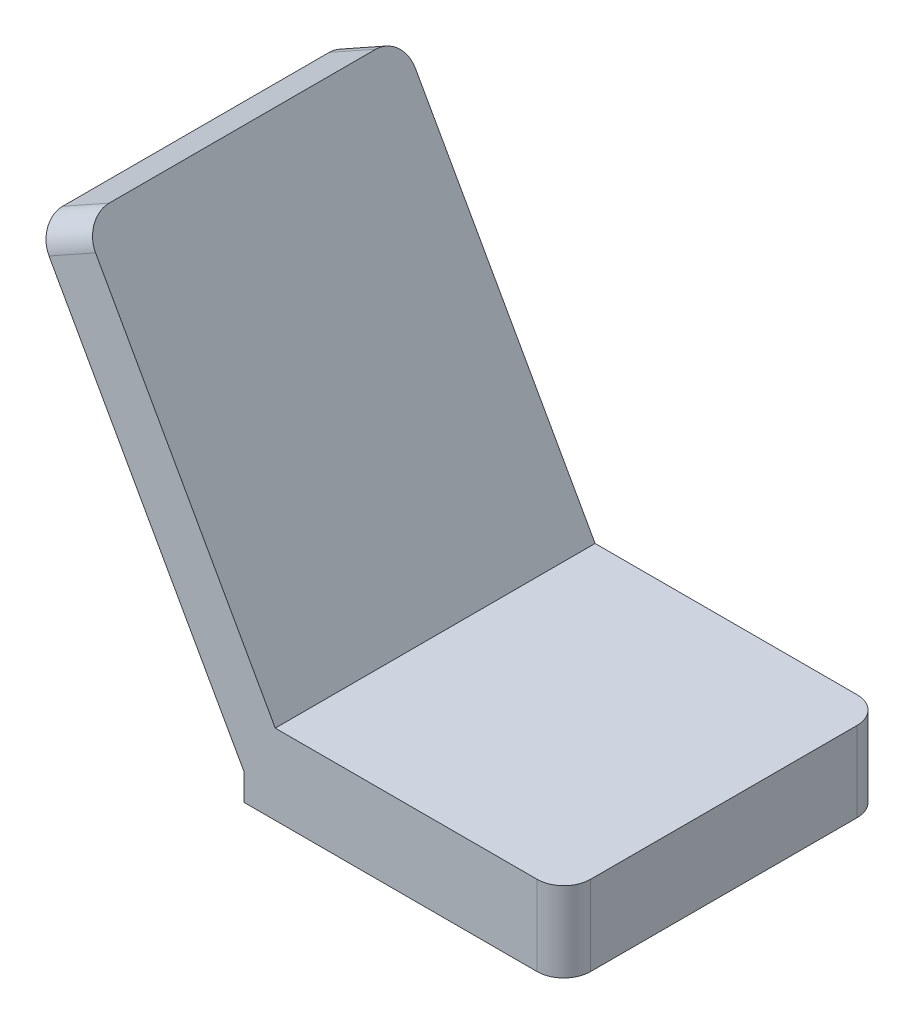
SolidWorks part; units mm, degrees
ref_plane "Front Plane" through (0, 0, 0) normal (0, 0, 1) x (1, 0, 0)
ref_plane "Top Plane" through (0, 0, 0) normal (0, 1, 0) x (1, 0, 0)
ref_plane "Right Plane" through (0, 0, 0) normal (1, 0, 0) x (0, 0, -1)
sketch "Sketch1" plane through (0, 0, 0) normal (0, 0, 1) x (1, 0, 0)
  line L0 (-98.2965, 0) -> (95.669, 0) construction
  line L1 (34.692, 0) -> (-25.308, 0)
  line L2 (-25.308, 0) -> (-64.3237, 69.8411)
  dimension "D1" = 60
  dimension "D2" = 80
extrude "Extrude-Thin2" add sketch "Sketch1" along normal blind 60 thin
sketch "Sketch2" plane through (0, 0, 0) normal (0, -1, 0) x (1, 0, 0)
  line L0 (34.692, 60) -> (34.692, 0) construction
  line L1 (-25.308, 60) -> (34.692, 60)
  line L2 (-25.308, 60) -> (-25.308, 0)
  line L3 (-25.308, 0) -> (34.692, 0)
  line L4 (34.692, 60) -> (34.692, 0)
extrude "Boss-Extrude1" add sketch "Sketch2" along normal blind 5
fillet "Fillet5" radius 5 1 edges at (-59.9586, 72.2796, 60)
fillet "Fillet6" radius 5 1 edges at (34.692, 2.5, 60)
fillet "Fillet7" radius 5 1 edges at (34.692, 2.5, 0)
fillet "Fillet8" radius 5 1 edges at (-59.9586, 72.2796, 0)
